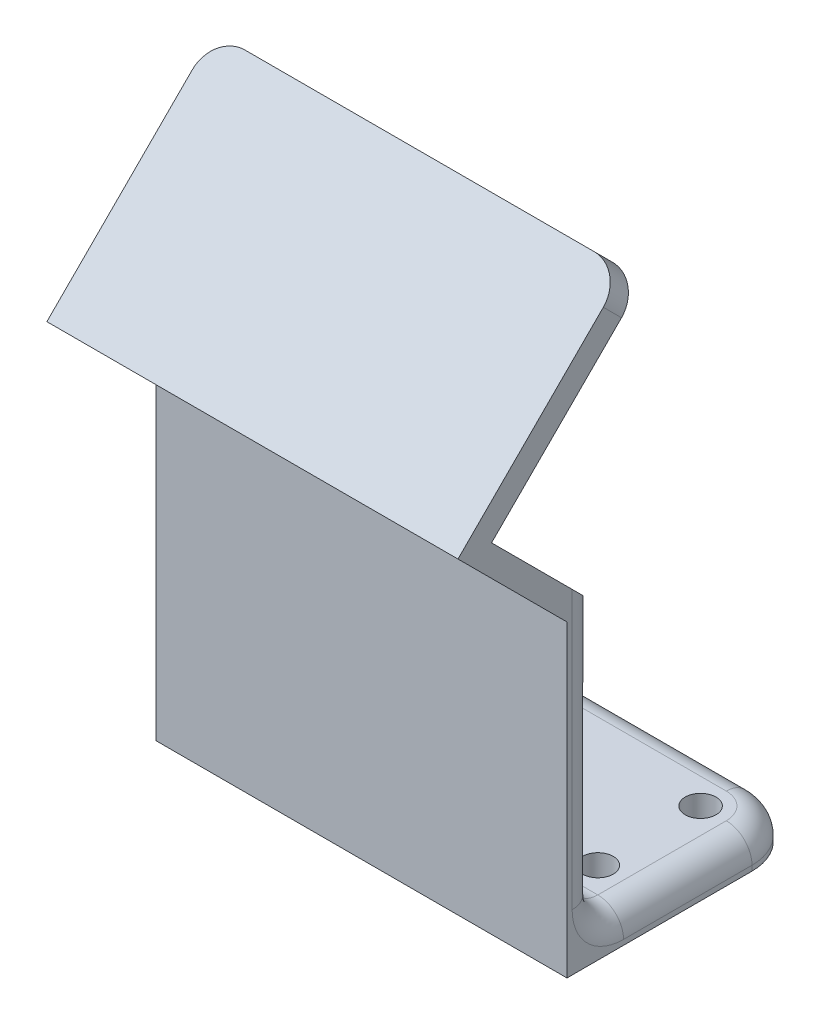
SolidWorks part; units mm, degrees
ref_plane "Front Plane" through (0, 0, 0) normal (0, 0, 1) x (1, 0, 0)
ref_plane "Top Plane" through (0, 0, 0) normal (0, 1, 0) x (1, 0, 0)
ref_plane "Right Plane" through (0, 0, 0) normal (1, 0, 0) x (0, 0, -1)
sketch "Sketch1" plane through (0, 0, 0) normal (0, 1, 0) x (1, 0, 0)
  line L0 (40, 0) -> (40, 15)
  line L1 (0, 0) -> (40, 0)
  line L2 (0, 0) -> (0, 15)
  line L3 (5, 20) -> (35, 20)
  line L4 (20, 0) -> (20, 20) construction
  arc A0 (0, 15) -> (5, 20) centre (5, 15) cw
  circle A1 centre (5, 15) radius 1.5
  circle A2 centre (5, 5) radius 1.5
  circle A3 centre (35, 15) radius 1.5
  circle A4 centre (35, 5) radius 1.5
  arc A5 (40, 15) -> (35, 20) centre (35, 15) ccw
  point P7 (0, 20)
  point P11 (5, 3.8159)
  point P12 (7.4672, 3.8159)
  dimension "D3" = 5
  dimension "D4" = 3
  dimension "D1" = 15
  dimension "D2" = 20
  dimension "D5" = 10
extrude "Boss-Extrude1" add sketch "Sketch1" along normal blind 3
sketch "Sketch2" plane through (0, 0, 0) normal (0, 0, 1) x (1, 0, 0)
  line L1 (0, 0) -> (40, 0)
  line L2 (0, 0) -> (0, 30)
  line L3 (0, 30) -> (40, 30)
  line L4 (40, 0) -> (40, 30)
  line L5 (40, 3) -> (40, 0) construction
  dimension "D1" = 30
extrude "Boss-Extrude2" add sketch "Sketch2" along normal blind 3
sketch "Sketch3" plane through (40, 0, 0) normal (1, 0, 0) x (0, 0, -1)
  line L0 (-3, 30) -> (-13.6066, 40.6066)
  line L1 (-13.6066, 40.6066) -> (-11.4853, 42.7279)
  line L2 (-10.3388, 40.3388) -> (0, 30)
  line L3 (0, 30) -> (-3, 30)
  line L4 (-3, 0) -> (-3, 30) construction
  line L5 (-11.4853, 42.7279) -> (2.6569, 56.8701)
  line L6 (2.6569, 56.8701) -> (4.4246, 55.1023)
  line L7 (4.4246, 55.1023) -> (-10.3388, 40.3388)
  point P11 (0, 0)
  dimension "D1" = 135
  dimension "D2" = 15
  dimension "D3" = 20
  dimension "D4" = 3
  dimension "D5" = 2.5
extrude "Boss-Extrude3" add sketch "Sketch3" against normal up to surface (40 mm away) up to face at (0, 11, -4)
sketch "Sketch4" plane through (0, 27.1066, 27.1066) normal (0, 0.7071, 0.7071) x (1, 0, 0)
  line L0 (0, 42.0919) -> (3, 42.0919)
  line L1 (3, 42.0919) -> (37, 42.0919)
  line L2 (0, 39.0919) -> (0, 19.0919)
  line L3 (0, 19.0919) -> (40, 19.0919)
  line L4 (40, 39.0919) -> (40, 19.0919)
  line L5 (0, 42.0919) -> (0, 39.0919)
  line L6 (37, 42.0919) -> (40, 42.0919)
  line L7 (40, 42.0919) -> (40, 39.0919)
  arc A0 (40, 39.0919) -> (37, 42.0919) centre (37, 39.0919) ccw
  arc A1 (0, 39.0919) -> (3, 42.0919) centre (3, 39.0919) cw
  point P10 (0, 42.0919)
  line M1 (0, 42.0919) -> (0, 19.0919)
  line M3 (40, 19.0919) -> (40, 42.0919)
  line M4 (40, 42.0919) -> (0, 42.0919)
  dimension "D1" = 3
extrude "Cut-Extrude1" cut sketch "Sketch4" against normal blind 3 contours A1 M1 M4 | A0 M3 M4
fillet "Fillet2" radius 2.5 9 edges at (20, 3, -20) (38.5355, 3, -18.5355) (1.4645, 3, -18.5355) (40, 3, -7.5) (0, 3, -7.5) (40, 16.5, 0) (20, 30, 0) (0, 16.5, 0) (20, 3, 0)
